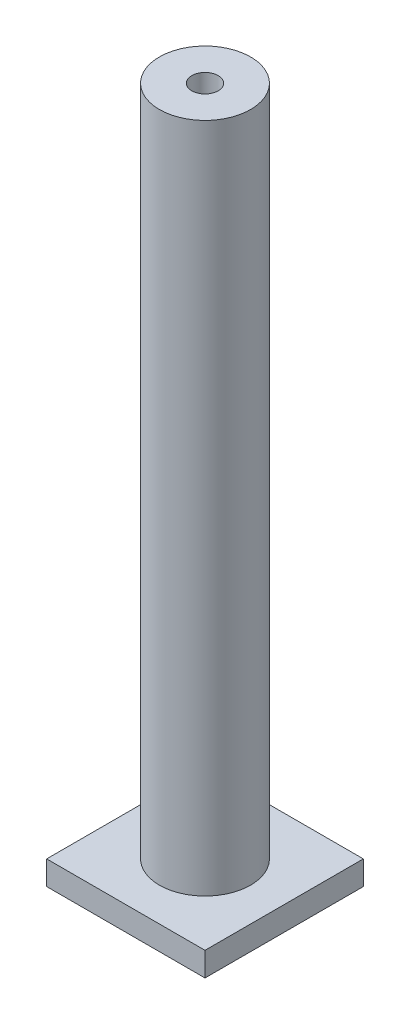
SolidWorks part; units mm, degrees
ref_plane "Front Plane" through (0, 0, 0) normal (0, 0, 1) x (1, 0, 0)
ref_plane "Top Plane" through (0, 0, 0) normal (0, 1, 0) x (1, 0, 0)
ref_plane "Right Plane" through (0, 0, 0) normal (1, 0, 0) x (0, 0, -1)
sketch "Sketch1" plane through (0, 0, 0) normal (0, 1, 0) x (1, 0, 0)
  line L0 (-7.7945, 6.8328) -> (8.7055, -9.6672) construction
  line L1 (-7.7945, 6.8328) -> (8.7055, 6.8328)
  line L2 (-7.7945, 6.8328) -> (-7.7945, -9.6672)
  line L3 (-7.7945, -9.6672) -> (8.7055, -9.6672)
  line L4 (8.7055, 6.8328) -> (8.7055, -9.6672)
  circle A0 centre (0.4555, -1.4172) radius 1.375
  circle A1 centre (0.4555, -1.4172) radius 4.75 construction
  dimension "D2" = 2.75
  dimension "D3" = 9.5
  dimension "D1" = 16.5
extrude "Boss-Extrude1" add sketch "Sketch1" along normal blind 2.5
sketch "Sketch2" plane through (0, 2.5, 0) normal (0, 1, 0) x (1, 0, 0)
  circle A0 centre (0.4555, -1.4172) radius 4.75 construction
  circle A1 centre (0.4555, -1.4172) radius 4.75
  circle A2 centre (0.4555, -1.4172) radius 1.375 construction
  circle A3 centre (0.4555, -1.4172) radius 1.375
extrude "Boss-Extrude2" add sketch "Sketch2" along normal blind 70
